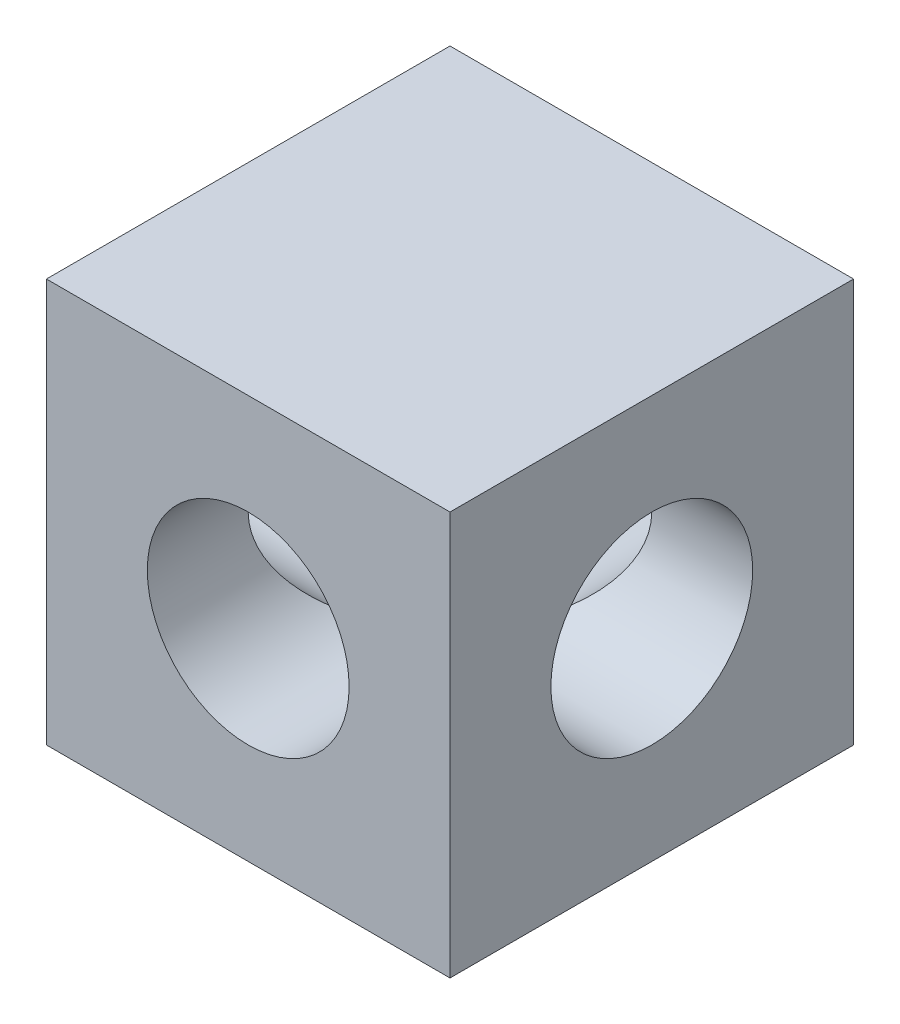
SolidWorks part; units mm, degrees
ref_plane "Front" through (0, 0, 0) normal (0, 0, 1) x (1, 0, 0)
ref_plane "Top" through (0, 0, 0) normal (0, 1, 0) x (-1, 0, 0)
ref_plane "Right" through (0, 0, 0) normal (1, 0, 0) x (0, 0, -1)
sketch "Sketch1" plane through (0, 0, 0) normal (0, 0, 1) x (1, 0, 0)
  line L0 (-9.525, -9.525) -> (9.525, -9.525)
  line L1 (-9.525, -9.525) -> (-9.525, 9.525)
  line L2 (9.525, 9.525) -> (-9.525, 9.525)
  line L3 (9.525, 9.525) -> (9.525, -9.525)
  line L4 (9.525, 9.525) -> (-9.525, -9.525) construction
  circle A0 centre (0, 0) radius 4.7625
extrude "Base-Extrude" add sketch "Sketch1" along normal mid plane 19.05
sketch "Sketch3" plane through (9.525, 0, 0) normal (1, 0, 0) x (0, 0, -1)
  circle A0 centre (0, 0) radius 4.7625
extrude "Cut-Extrude1" cut sketch "Sketch3" against normal through all
scale "Scale1" scale about centroid uniform scaling yes scale factor 0.65
